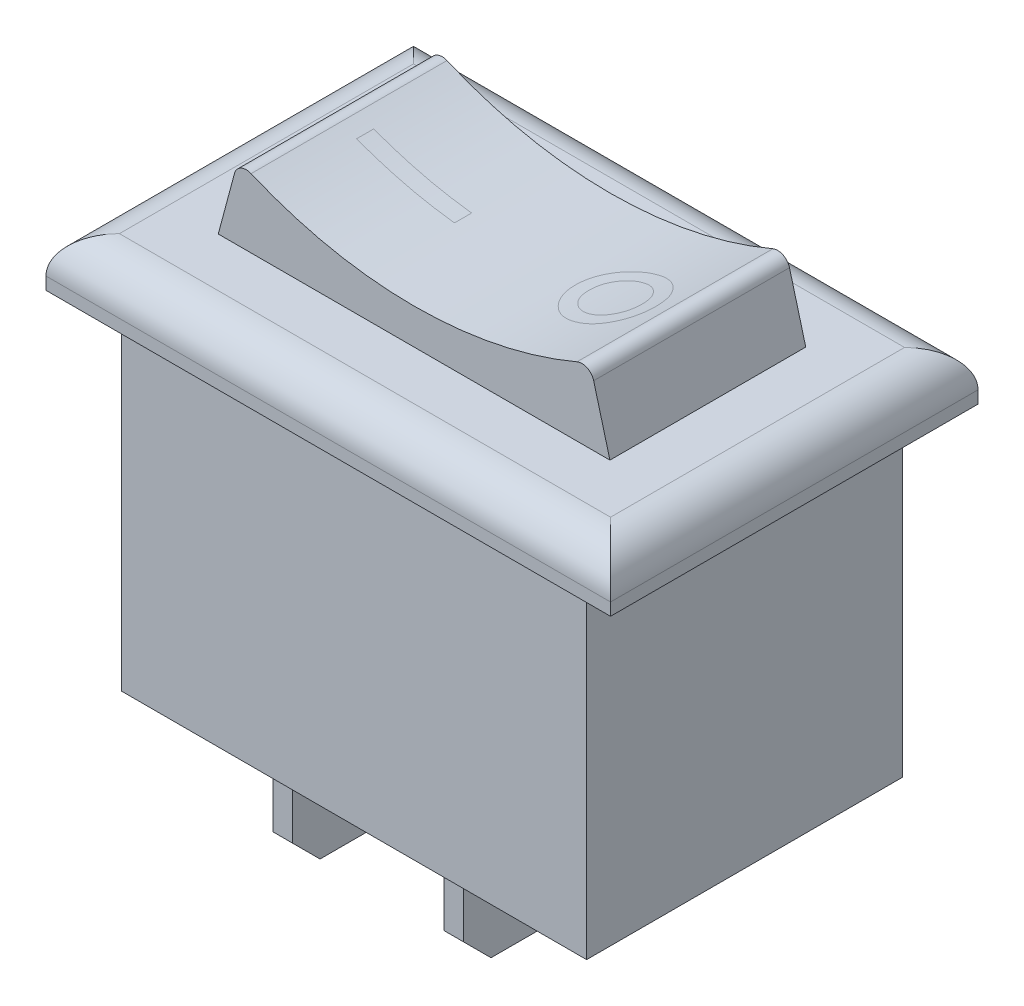
SolidWorks part; units mm, degrees
ref_plane "Front Plane" through (0, 0, 0) normal (0, 0, 1) x (1, 0, 0)
ref_plane "Top Plane" through (0, 0, 0) normal (0, 1, 0) x (1, 0, 0)
ref_plane "Right Plane" through (0, 0, 0) normal (1, 0, 0) x (0, 0, -1)
sketch "Sketch1" plane through (0, 0, 0) normal (0, 0, 1) x (1, 0, 0)
  line L0 (-11.5316, 0) -> (-9.4996, 0)
  line L1 (-9.4996, 0) -> (9.4996, 0) construction
  line L2 (-9.4996, 0) -> (-9.4996, -13.6906)
  line L3 (-9.4996, -13.6906) -> (9.4996, -13.6906)
  line L4 (9.4996, 0) -> (9.4996, -13.6906)
  line L5 (11.5316, 2.0066) -> (-11.5316, 2.0066)
  line L6 (11.5316, 2.0066) -> (11.5316, 0)
  line L7 (11.5316, 0) -> (-11.5316, 0) construction
  line L8 (-11.5316, 2.0066) -> (-11.5316, 0)
  line L9 (11.5316, 0) -> (9.4996, 0)
  point P9 (0, 0)
  point P10 (0, 0)
  point P11 (0, 2.0066)
  dimension "D1" = 18.9992
  dimension "D2" = 13.6906
  dimension "D3" = 2.0066
  dimension "D4" = 2.032
extrude "body" add sketch "Sketch1" along normal mid plane 15.0114
sketch "Sketch2" plane through (11.5316, 0, 0) normal (1, 0, 0) x (0, 0, -1)
  line L0 (-7.5057, 0) -> (7.5057, 0) construction
  line L1 (-7.5057, -13.6906) -> (-6.4516, -13.6906)
  line L2 (-7.5057, -13.6906) -> (-7.5057, 0)
  line L3 (-7.5057, 0) -> (-6.4516, 0)
  line L4 (-6.4516, -13.6906) -> (-6.4516, 0)
  line L6 (7.5057, -13.6906) -> (6.4516, -13.6906)
  line L7 (7.5057, -13.6906) -> (7.5057, 0)
  line L8 (7.5057, 0) -> (6.4516, 0)
  line L9 (6.4516, -13.6906) -> (6.4516, 0)
  dimension "D1" = 12.9032
extrude "narrow" cut sketch "Sketch2" against normal through all
fillet "panel_fillet" radius 1.5 4 edges at (11.5316, 2.0066, 0) (0, 2.0066, 7.5057) (-11.5316, 2.0066, 0) (0, 2.0066, -7.5057)
sketch "Sketch4" plane through (0, 0, 6.4516) normal (0, 0, 1) x (1, 0, 0)
  line L0 (-9.4996, -13.6906) -> (9.4996, -13.6906) construction
  line L1 (-7.3787, -13.6906) -> (-6.5913, -13.6906)
  line L2 (-7.3787, -13.6906) -> (-7.3787, -20.7772)
  line L3 (-7.3787, -20.7772) -> (-6.5913, -20.7772)
  line L4 (-6.5913, -13.6906) -> (-6.5913, -20.7772)
  line L5 (0, 0) -> (0, -23.1558) construction
  line L6 (-0.3937, -13.6906) -> (0.3937, -13.6906)
  line L7 (-0.3937, -13.6906) -> (-0.3937, -20.7772)
  line L8 (-0.3937, -20.7772) -> (0.3937, -20.7772)
  line L9 (0.3937, -13.6906) -> (0.3937, -20.7772)
  line L10 (-9.4996, 0) -> (9.4996, 0) construction
  point P14 (0, -20.7772)
  point P15 (-6.985, -20.7772)
  dimension "D1" = 7.0866
  dimension "D2" = 0.7874
  dimension "D3" = 6.985
extrude "terminals" add sketch "Sketch4" against normal up to surface (12.9032 mm away) separate body up to face at (0, -6.8453, -6.4516)
sketch "Sketch5" plane through (-9.4996, 0, 0) normal (-1, 0, 0) x (0, 0, 1)
  line L0 (-6.4516, -20.7772) -> (6.4516, -20.7772) construction
  line L1 (-6.4516, -13.6906) -> (6.4516, -13.6906) construction
  line L2 (-6.4516, -20.7772) -> (6.4516, -20.7772) construction
  line L3 (-2.3749, -19.6523) -> (-1.25, -20.7772)
  line L4 (-2.3749, -13.6906) -> (-2.3749, -19.6523)
  line L5 (-1.0825, -17.1522) -> (-0.6495, -17.9022)
  line L6 (-2.3749, -13.6906) -> (2.3749, -13.6906)
  line L7 (2.3749, -20.7772) -> (-2.3749, -20.7772) construction
  line L8 (-1.25, -20.7772) -> (1.25, -20.7772)
  line L9 (2.3749, -13.6906) -> (2.3749, -19.6523)
  line L10 (1.0825, -17.1522) -> (0.6495, -17.9022)
  line L11 (0, -16.5272) -> (0, -17.5272) construction
  line L12 (1.25, -20.7772) -> (2.3749, -19.6523)
  arc A0 (1.0825, -17.1522) -> (-1.0825, -17.1522) centre (0, -16.5272) ccw
  arc A1 (-0.6495, -17.9022) -> (0.6495, -17.9022) centre (0, -17.5272) ccw
  point P7 (0, -13.6906)
  point P13 (0, -20.7772)
  point P16 (0, -18.2772)
  point P17 (0, -15.2772)
  point P25 (0, -20.7772)
  dimension "D2" = 2.5
  dimension "D3" = 1.5
  dimension "D1" = 4.7498
  dimension "D4" = 3
  dimension "D5" = 2.5
  dimension "D6" = 2.5
extrude "terminal_trim" cut sketch "Sketch5" against normal through all flip side to cut
ref_plane "Plane1" through (0, 0, 0) normal (0, 0, 1) x (1, 0, 0)
sketch "Sketch6" plane through (0, 0, 0) normal (0, 0, 1) x (1, 0, 0)
  line L0 (-7.3363, 4.4836) -> (-8, 2.0066)
  line L1 (-10.0316, 2.0066) -> (10.0316, 2.0066) construction
  line L2 (7.3363, 4.4836) -> (8, 2.0066)
  line L3 (-8, 2.0066) -> (8, 2.0066)
  line L4 (-9.4996, 0) -> (9.4996, 0) construction
  arc A0 (-6.6575, 4.8142) -> (6.6575, 4.8142) centre (0, 20.4564) ccw
  arc A1 (6.6575, 4.8142) -> (7.3363, 4.4836) centre (6.8533, 4.3542) cw
  arc A2 (-6.6575, 4.8142) -> (-7.3363, 4.4836) centre (-6.8533, 4.3542) ccw
  point P9 (0, 0)
  point P10 (0, 2.0066)
  point P14 (7.1847, 5.0493)
  dimension "D3" = 17
  dimension "D6" = 0.5
  dimension "D1" = 75
  dimension "D2" = 75
  dimension "D4" = 16
  dimension "D5" = 3.15
extrude "toggle" add sketch "Sketch6" along normal blind 4 and the other way blind 4
sketch "Sketch7" plane through (0, 0, 0) normal (0, 1, 0) x (1, 0, 0)
  line L0 (-10.4496, 0) -> (10.4496, 0) construction
  line L1 (-6, 0.35) -> (-2, 0.35)
  line L2 (-6, 0.35) -> (-6, -0.35)
  line L3 (-6, -0.35) -> (-2, -0.35)
  line L4 (-2, 0.35) -> (-2, -0.35)
  line L5 (-8, 4) -> (-8, -4) construction
  text T0 "<b> O</b>"
  point P5 (-6, 0)
  dimension "D1" = 0.7
  dimension "D2" = 4
  dimension "D3" = 2
split line "Split Line1"
sketch "Sketch8" plane through (0, 0, -6.4516) normal (0, 0, -1) x (-1, 0, 0)
  text T0 "10A\r\n125v" font "DS ISO 1" height 3
  dimension "D1" = 6
  dimension "D2" = 4.5
split line "Split Line2"
